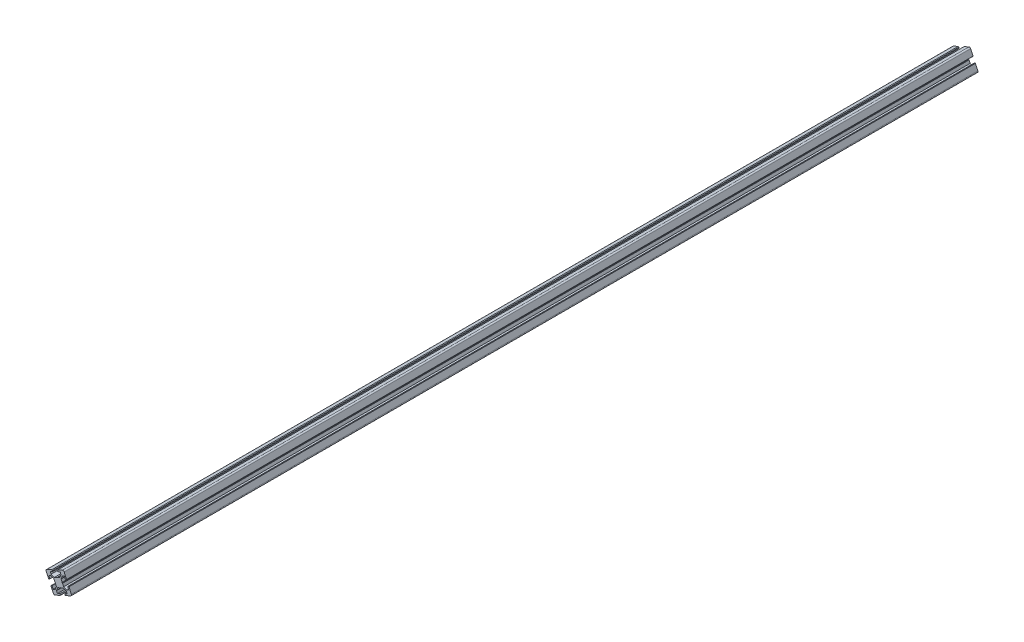
SolidWorks part; units mm, degrees
ref_plane "Front" through (0, 0, 0) normal (0, 0, 1) x (1, 0, 0)
ref_plane "Top" through (0, 0, 0) normal (0, 1, 0) x (1, 0, 0)
ref_plane "Right" through (0, 0, 0) normal (1, 0, 0) x (0, 0, -1)
sketch "Sketch1" plane through (0, 0, 0) normal (0, 0, 1) x (1, 0, 0)
  line L0 (9.5406, 11.1432) -> (-0.9204, 6.3464)
  line L1 (-0.9204, 6.3464) -> (-1.5357, 4.6889)
  line L2 (-1.5357, 4.6889) -> (-0.8897, 3.2801)
  line L3 (-0.8897, 3.2801) -> (4.6629, 5.8262)
  line L4 (4.6629, 5.8262) -> (6.6094, 1.5812)
  line L5 (6.6094, 1.5812) -> (4.0846, -5.2201)
  line L6 (4.0846, -5.2201) -> (-1.09, -7.5929)
  line L7 (-1.09, -7.5929) -> (-1.5761, -8.2779)
  line L8 (-1.5761, -8.2779) -> (-2.4125, -8.1993)
  line L9 (-2.4125, -8.1993) -> (-7.587, -10.5721)
  line L10 (-7.587, -10.5721) -> (-14.3883, -8.0473)
  line L11 (-14.3883, -8.0473) -> (-16.3348, -3.8022)
  line L12 (-16.3348, -3.8022) -> (-10.7823, -1.2561)
  line L13 (-10.7823, -1.2561) -> (-11.4283, 0.1527)
  line L14 (-11.4283, 0.1527) -> (-13.0858, 0.768)
  line L15 (-13.0858, 0.768) -> (-23.5467, -4.0288)
  line L16 (-24.9248, -7.7411) -> (-19.848, -18.8126)
  line L17 (-19.2912, -19.0193) -> (-17.1278, -18.0273)
  line L18 (-17.1278, -18.0273) -> (-19.6078, -12.6188)
  line L19 (-19.6078, -12.6188) -> (-15.3627, -10.6722)
  line L20 (-15.3627, -10.6722) -> (-8.5615, -13.197)
  line L21 (-8.5615, -13.197) -> (-6.1887, -18.3716)
  line L22 (-6.1887, -18.3716) -> (-5.5037, -18.8578)
  line L23 (-5.5037, -18.8578) -> (-5.5823, -19.6941)
  line L24 (-5.5823, -19.6941) -> (-3.2095, -24.8687)
  line L25 (-3.2095, -24.8687) -> (-5.7343, -31.6699)
  line L26 (-5.7343, -31.6699) -> (-9.9794, -33.6165)
  line L27 (-9.9794, -33.6165) -> (-12.4594, -28.208)
  line L28 (-12.4594, -28.208) -> (-14.6228, -29.2)
  line L29 (-14.8295, -29.7569) -> (-9.7527, -40.8284)
  line L30 (-6.0405, -42.2065) -> (5.031, -37.1297)
  line L31 (5.2377, -36.5728) -> (4.2457, -34.4094)
  line L32 (4.2457, -34.4094) -> (-1.1628, -36.8895)
  line L33 (-1.1628, -36.8895) -> (-3.1093, -32.6444)
  line L34 (-3.1093, -32.6444) -> (-0.5845, -25.8431)
  line L35 (-0.5845, -25.8431) -> (4.59, -23.4704)
  line L36 (4.59, -23.4704) -> (5.0762, -22.7854)
  line L37 (5.0762, -22.7854) -> (5.9125, -22.8639)
  line L38 (5.9125, -22.8639) -> (11.0871, -20.4911)
  line L39 (11.0871, -20.4911) -> (17.8884, -23.016)
  line L40 (17.8884, -23.016) -> (19.8349, -27.261)
  line L41 (19.8349, -27.261) -> (14.4264, -29.7411)
  line L42 (14.4264, -29.7411) -> (15.4184, -31.9045)
  line L43 (15.9753, -32.1112) -> (27.0468, -27.0344)
  line L44 (28.4249, -23.3221) -> (23.3481, -12.2506)
  line L45 (22.7912, -12.0439) -> (20.6278, -13.0359)
  line L46 (20.6278, -13.0359) -> (23.1079, -18.4444)
  line L47 (23.1079, -18.4444) -> (18.8628, -20.391)
  line L48 (18.8628, -20.391) -> (12.0616, -17.8662)
  line L49 (12.0616, -17.8662) -> (9.6888, -12.6916)
  line L50 (9.6888, -12.6916) -> (9.0038, -12.2054)
  line L51 (9.0038, -12.2054) -> (9.0823, -11.3691)
  line L52 (9.0823, -11.3691) -> (6.7096, -6.1945)
  line L53 (6.7096, -6.1945) -> (9.2344, 0.6067)
  line L54 (9.2344, 0.6067) -> (13.4795, 2.5533)
  line L55 (13.4795, 2.5533) -> (15.9595, -2.8552)
  line L56 (15.9595, -2.8552) -> (18.1229, -1.8632)
  line L57 (18.3296, -1.3064) -> (13.2528, 9.7652)
  arc A0 (13.2528, 9.7652) -> (9.5406, 11.1432) centre (10.7076, 8.5981) ccw
  arc A1 (-23.5467, -4.0288) -> (-24.9248, -7.7411) centre (-22.3796, -6.574) ccw
  arc A2 (-19.848, -18.8126) -> (-19.2912, -19.0193) centre (-19.4662, -18.6375) ccw
  arc A3 (-14.6228, -29.2) -> (-14.8295, -29.7569) centre (-14.4478, -29.5818) ccw
  arc A4 (-9.7527, -40.8284) -> (-6.0405, -42.2065) centre (-7.2076, -39.6613) ccw
  arc A5 (5.031, -37.1297) -> (5.2377, -36.5728) centre (4.856, -36.7479) ccw
  arc A6 (15.4184, -31.9045) -> (15.9753, -32.1112) centre (15.8002, -31.7294) ccw
  arc A7 (27.0468, -27.0344) -> (28.4249, -23.3221) centre (25.8797, -24.4892) ccw
  arc A8 (23.3481, -12.2506) -> (22.7912, -12.0439) centre (22.9663, -12.4257) ccw
  arc A9 (18.1229, -1.8632) -> (18.3296, -1.3064) centre (17.9479, -1.4814) ccw
extrude "Boss-Extrude1" add sketch "Sketch1" along normal blind 1916.03
